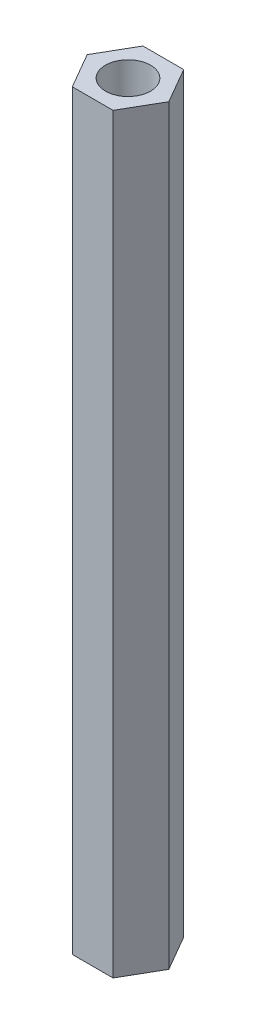
SolidWorks part; units mm, degrees
ref_plane "Front Plane" through (0, 0, 0) normal (0, 0, 1) x (1, 0, 0)
ref_plane "Top Plane" through (0, 0, 0) normal (0, 1, 0) x (1, 0, 0)
ref_plane "Right Plane" through (0, 0, 0) normal (1, 0, 0) x (0, 0, -1)
sketch "Sketch2" plane through (0, 0, 0) normal (0, 1, 0) x (1, 0, 0)
  line L1 (2.7135, 0) -> (1.3568, 2.35)
  line L2 (1.3568, 2.35) -> (-1.3568, 2.35)
  line L3 (-1.3568, 2.35) -> (-2.7135, 0)
  line L4 (-2.7135, 0) -> (-1.3568, -2.35)
  line L5 (-1.3568, -2.35) -> (1.3568, -2.35)
  line L6 (1.3568, -2.35) -> (2.7135, 0)
  circle A0 centre (0, 0) radius 2.35 construction
  circle A1 centre (0, 0) radius 1.5
  dimension "D1" = 4.7
  dimension "D3" = 3
  dimension "D2" = 2.35
extrude "Boss-Extrude1" add sketch "Sketch2" along normal blind 50
